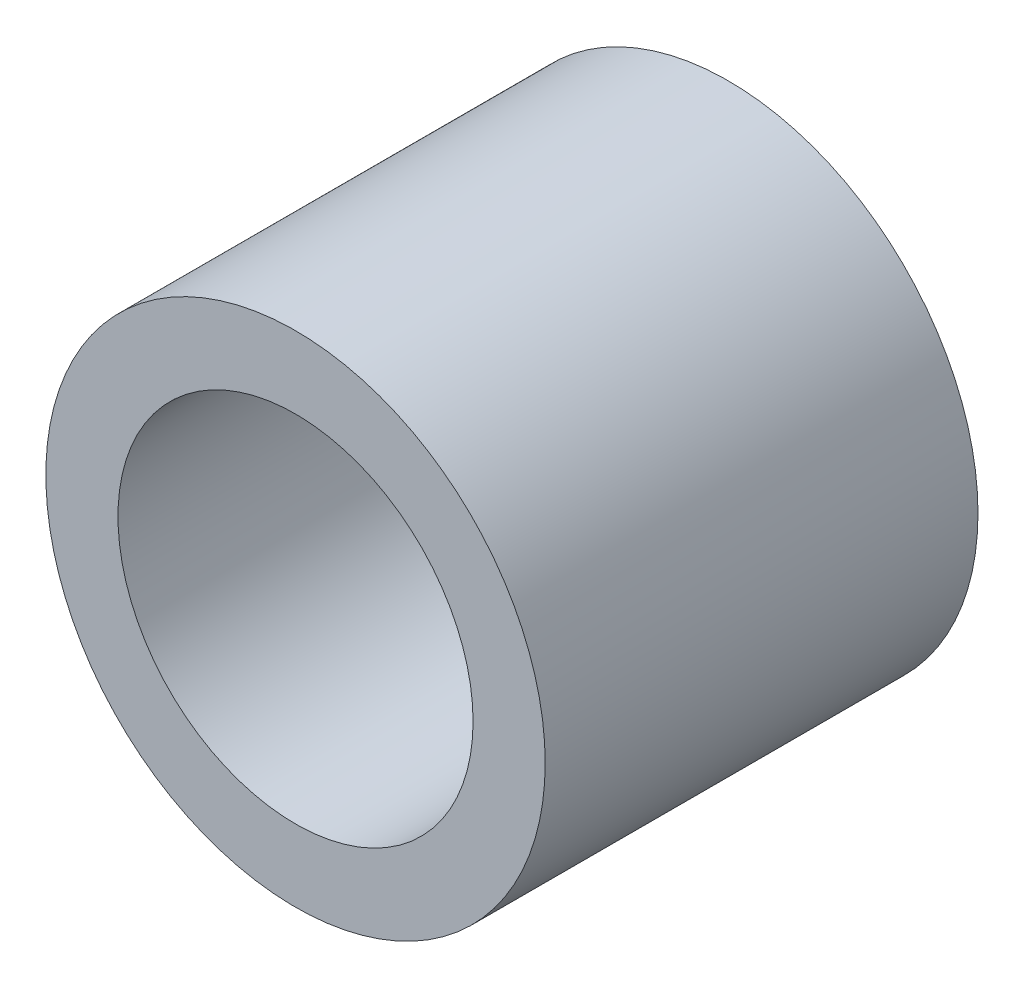
SolidWorks part; units mm, degrees
ref_plane "Front Plane" through (0, 0, 0) normal (0, 0, 1) x (1, 0, 0)
ref_plane "Top Plane" through (0, 0, 0) normal (0, 1, 0) x (1, 0, 0)
ref_plane "Right Plane" through (0, 0, 0) normal (1, 0, 0) x (0, 0, -1)
sketch "Sketch1" plane through (0, 0, 0) normal (0, 0, 1) x (1, 0, 0)
  line L5 (15.9099, -15.9099) -> (-15.9099, 15.9099) construction
  line L6 (15.9099, 15.9099) -> (-15.9099, -15.9099) construction
  circle A0 centre (0, 0) radius 16
  circle A1 centre (0, 0) radius 22.5
  point P0 (0, 0)
  dimension "D3" = 32
  dimension "D4" = 45
extrude "Boss-Extrude1" add sketch "Sketch1" along normal blind 39
